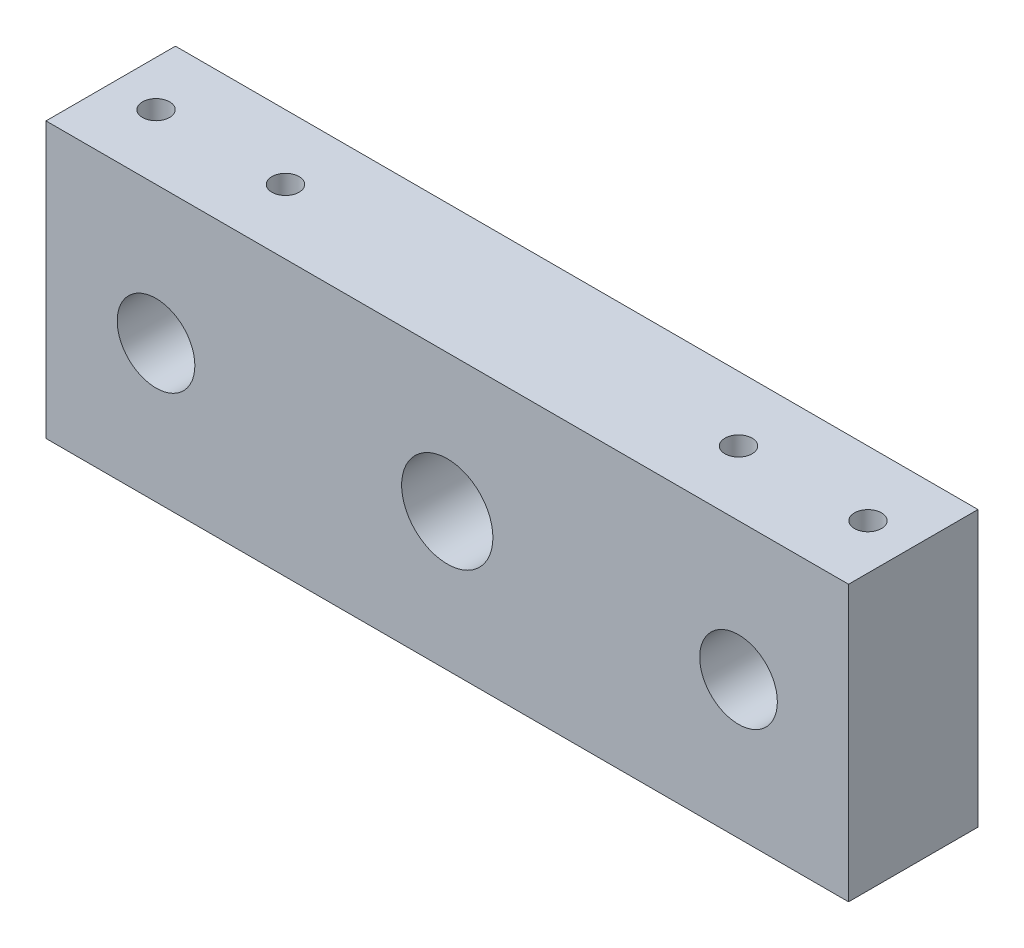
SolidWorks part; units mm, degrees
material "6061 Alloy"
ref_plane "Front Plane" through (0, 0, 0) normal (0, 0, 1) x (1, 0, 0)
ref_plane "Top Plane" through (0, 0, 0) normal (0, 1, 0) x (1, 0, 0)
ref_plane "Right Plane" through (0, 0, 0) normal (1, 0, 0) x (0, 0, -1)
sketch "Sketch1" plane through (0, 0, 0) normal (0, 0, 1) x (1, 0, 0)
  line L0 (-19.8312, 21.25) -> (164.2226, 21.25) construction
  line L1 (0, 0) -> (124, 0)
  line L2 (0, 0) -> (0, 42.5)
  line L3 (0, 42.5) -> (124, 42.5)
  line L4 (124, 0) -> (124, 42.5)
  line L6 (107, 85.9264) -> (107, -35.3051) construction
  line L8 (62, 85.9264) -> (62, -33.269) construction
  line L10 (17, 100.7234) -> (17, -28.8524) construction
  circle A0 centre (17, 21.25) radius 6
  circle A1 centre (107, 21.25) radius 6
  circle A2 centre (62, 21.25) radius 5
  dimension "D5" = 12
  dimension "D6" = 10
  dimension "D1" = 42.5
  dimension "D2" = 124
  dimension "D3" = 17
  dimension "D4" = 17
extrude "Boss-Extrude1" add sketch "Sketch1" along normal blind 20
sketch "Sketch2" plane through (0, 0, 0) normal (0, -1, 0) x (1, 0, 0)
  line L0 (-31.5475, 10) -> (158.7129, 10) construction
  line L1 (0, 0) -> (124, 0) construction
  line L2 (0, 20) -> (124, 20) construction
  line L3 (0, 20) -> (0, 0) construction
  line L4 (124, 20) -> (124, 0) construction
  circle A0 centre (7, 10) radius 2.1
  circle A1 centre (27, 10) radius 2.1
  circle A2 centre (97, 10) radius 2.1
  circle A3 centre (117, 10) radius 2.1
  circle A4 centre (17, 10) radius 2.1
  circle A5 centre (107, 10) radius 2.1
  dimension "D1" = 4.2
  dimension "D7" = 17
  dimension "D2" = 7
  dimension "D3" = 27
  dimension "D4" = 7
  dimension "D5" = 27
  dimension "D6" = 17
extrude "Cut-Extrude1" cut sketch "Sketch2" against normal up to next
sketch "Sketch3" plane through (0, 0, 20) normal (0, 0, 1) x (1, 0, 0)
  circle A0 centre (62, 21.25) radius 7.05
  dimension "D1" = 14.1
extrude "Cut-Extrude2" cut sketch "Sketch3" against normal offset from surface (16 mm away) 4 up to face at (113, 21.25, 0)
